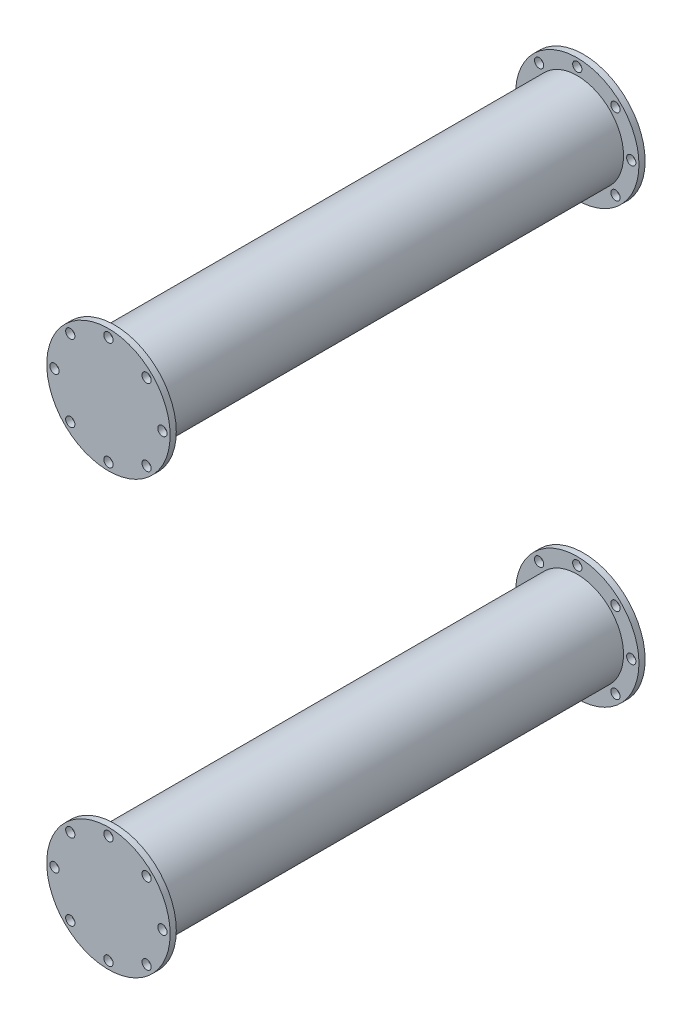
SolidWorks part; units mm, degrees
material "Plain Carbon Steel"
ref_plane "Front Plane" through (0, 0, 0) normal (0, 0, 1) x (1, 0, 0)
ref_plane "Top Plane" through (0, 0, 0) normal (0, 1, 0) x (1, 0, 0)
ref_plane "Right Plane" through (0, 0, 0) normal (1, 0, 0) x (0, 0, -1)
sketch "Sketch1" plane through (0, 0, 0) normal (0, 0, 1) x (1, 0, 0)
  circle A0 centre (0, 170) radius 20
  circle A2 centre (0, 187.5) radius 1.5
  circle A3 centre (12.3744, 182.3744) radius 1.5
  circle A4 centre (17.5, 170) radius 1.5
  circle A5 centre (12.3744, 157.6256) radius 1.5
  circle A6 centre (0, 152.5) radius 1.5
  circle A7 centre (-12.3744, 157.6256) radius 1.5
  circle A8 centre (-17.5, 170) radius 1.5
  circle A9 centre (-12.3744, 182.3744) radius 1.5
  circle A10 centre (0, 30) radius 20
  circle A11 centre (0, 47.5) radius 1.5
  circle A12 centre (12.3744, 42.3744) radius 1.5
  circle A13 centre (17.5, 30) radius 1.5
  circle A14 centre (12.3744, 17.6256) radius 1.5
  circle A15 centre (0, 12.5) radius 1.5
  circle A16 centre (-12.3744, 17.6256) radius 1.5
  circle A17 centre (-17.5, 30) radius 1.5
  circle A18 centre (-12.3744, 42.3744) radius 1.5
  point P24 (0, 170)
  point P43 (0, 30)
  dimension "D1" = 40
  dimension "D3" = 3
  dimension "D4" = 17.5
  dimension "D5" = 17.5
  dimension "D6" = 2
extrude "Boss-Extrude1" add sketch "Sketch1" along normal blind 2
sketch "Sketch2" plane through (0, 0, 2) normal (0, 0, 1) x (1, 0, 0)
  circle A0 centre (0, 170) radius 15
  circle A1 centre (0, 30) radius 15
  dimension "D1" = 30
  dimension "D2" = 30
extrude "Boss-Extrude2" add sketch "Sketch2" along normal blind 150
sketch "Sketch4" plane through (0, 0, 152) normal (0, 0, 1) x (1, 0, 0)
  circle A0 centre (0, 170) radius 20
  circle A2 centre (0, 187.5) radius 1.5
  circle A3 centre (12.3744, 182.3744) radius 1.5
  circle A4 centre (17.5, 170) radius 1.5
  circle A5 centre (12.3744, 157.6256) radius 1.5
  circle A6 centre (0, 152.5) radius 1.5
  circle A7 centre (-12.3744, 157.6256) radius 1.5
  circle A8 centre (-17.5, 170) radius 1.5
  circle A9 centre (-12.3744, 182.3744) radius 1.5
  circle A19 centre (0, 170) radius 15 construction
  circle A21 centre (0, 30) radius 20
  circle A22 centre (0, 47.5) radius 1.5
  circle A23 centre (12.3744, 42.3744) radius 1.5
  circle A24 centre (17.5, 30) radius 1.5
  circle A25 centre (12.3744, 17.6256) radius 1.5
  circle A26 centre (0, 12.5) radius 1.5
  circle A27 centre (-12.3744, 17.6256) radius 1.5
  circle A28 centre (-17.5, 30) radius 1.5
  circle A29 centre (-12.3744, 42.3744) radius 1.5
  point P24 (0, 170)
  point P40 (0, 30)
  dimension "D1" = 40
  dimension "D2" = 0
  dimension "D3" = 3
  dimension "D7" = 13.3939
  dimension "D9" = 0
  dimension "D4" = 17.5
  dimension "D5" = 17.5
  dimension "D8" = 17.5
  dimension "D10" = 2
  dimension "D6" = 8
extrude "Boss-Extrude3" add sketch "Sketch4" along normal blind 2
